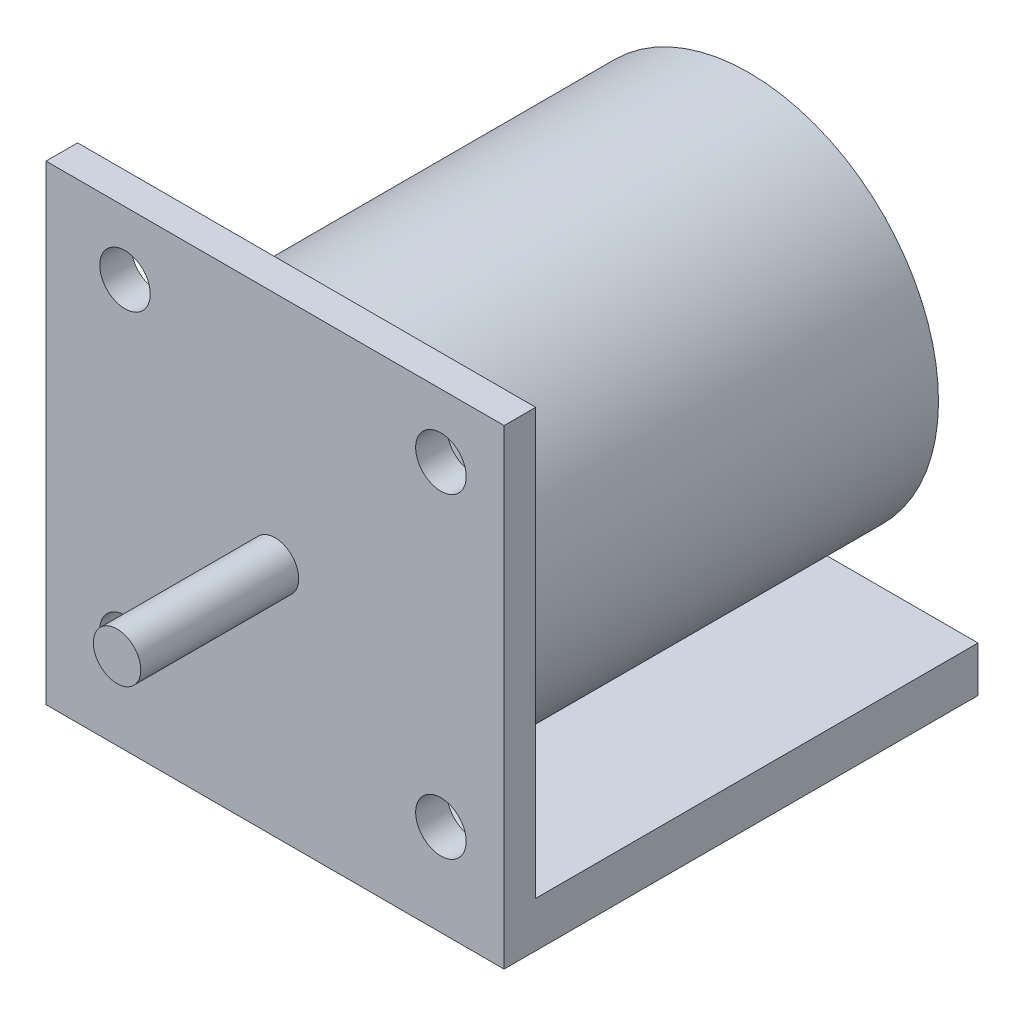
SolidWorks part; units mm, degrees
ref_plane "Front Plane" through (0, 0, 0) normal (0, 0, 1) x (1, 0, 0)
ref_plane "Top Plane" through (0, 0, 0) normal (0, 1, 0) x (1, 0, 0)
ref_plane "Right Plane" through (0, 0, 0) normal (1, 0, 0) x (0, 0, -1)
sketch "Sketch1" plane through (0, 0, 0) normal (0, 0, 1) x (1, 0, 0)
  line L1 (-18.415, -18.923) -> (18.415, -18.923)
  line L2 (-18.415, -18.923) -> (-18.415, 18.923)
  line L3 (-18.415, 18.923) -> (18.415, 18.923)
  line L4 (18.415, -18.923) -> (18.415, 18.923)
  line L5 (-18.415, -18.923) -> (18.415, 18.923) construction
  line L6 (-18.415, 18.923) -> (18.415, -18.923) construction
  point P0 (0, 0)
  dimension "D1" = 36.83
  dimension "D2" = 37.846
extrude "Boss-Extrude1" add sketch "Sketch1" along normal blind 2.54
sketch "Sketch2" plane through (0, 0, 2.54) normal (0, 0, 1) x (1, 0, 0)
  circle A0 centre (0, 0) radius 1.905
extrude "Boss-Extrude2" add sketch "Sketch2" along normal blind 12.7
sketch "Sketch3" plane through (0, 0, 0) normal (0, 0, -1) x (-1, 0, 0)
  circle A0 centre (0, 0) radius 15.24
extrude "Boss-Extrude3" add sketch "Sketch3" along normal blind 35.56
sketch "Sketch4" plane through (0, 0, 0) normal (0, 0, -1) x (-1, 0, 0)
  line L0 (-18.415, -18.923) -> (-18.415, 18.923) construction
  line L1 (18.415, -18.923) -> (-18.415, -18.923)
  line L2 (18.415, -18.923) -> (18.415, -15.2656)
  line L3 (18.415, -15.2656) -> (-18.415, -15.2656)
  line L4 (-18.415, -18.923) -> (-18.415, -15.2656)
extrude "Boss-Extrude4" add sketch "Sketch4" along normal blind 35.56
sketch "Sketch5" plane through (0, 0, 2.54) normal (0, 0, 1) x (1, 0, 0)
  line L0 (18.415, -18.923) -> (18.415, 18.923) construction
  line L1 (18.415, 18.923) -> (-18.415, 18.923) construction
  circle A0 centre (13.335, 13.843) radius 2.032
  circle A1 centre (-12.065, 13.843) radius 2.032
  circle A2 centre (-12.065, -11.557) radius 2.032
  circle A3 centre (13.335, -11.557) radius 2.032
  dimension "D1" = 5.08
  dimension "D2" = 5.08
  dimension "D3" = 2
  dimension "D4" = 2
extrude "Cut-Extrude1" cut sketch "Sketch5" against normal blind 35.56
